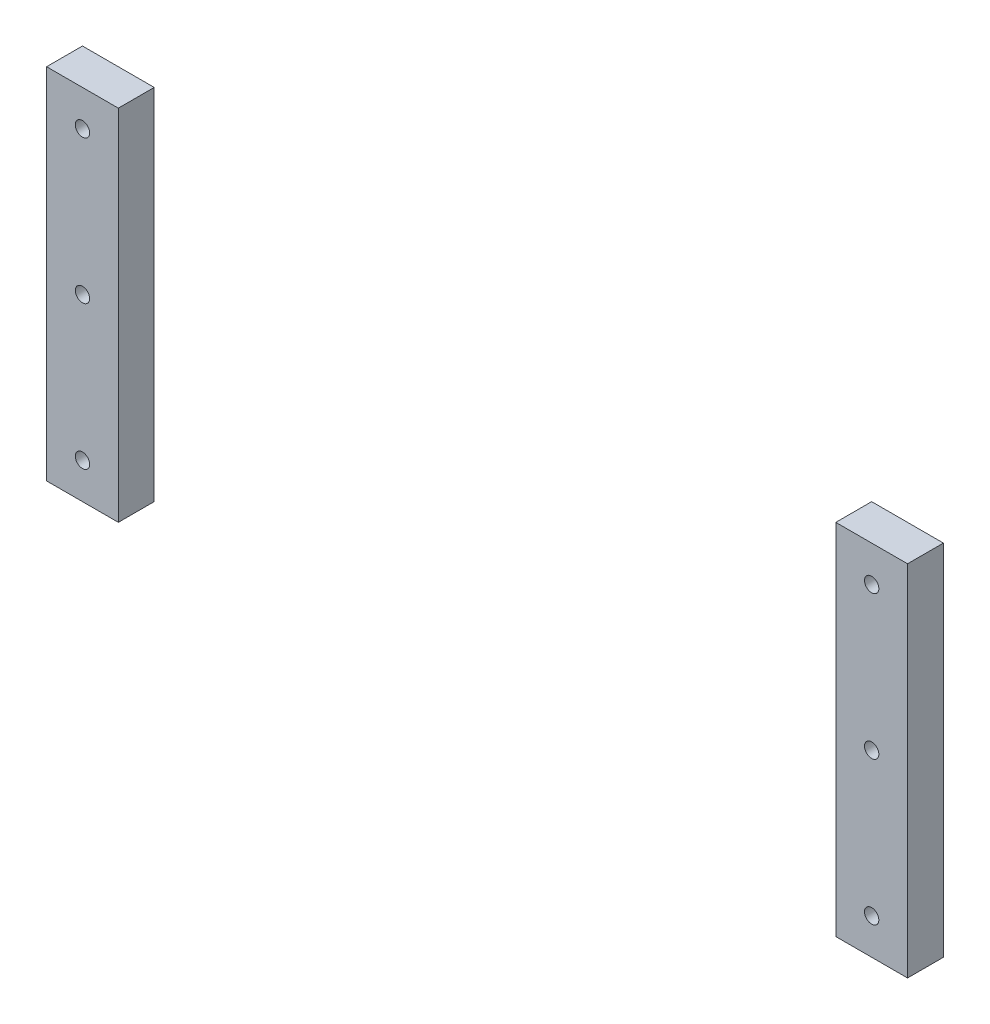
SolidWorks part; units mm, degrees
material "Cast Alloy Steel"
ref_plane "Front Plane" through (0, 0, 0) normal (0, 0, 1) x (1, 0, 0)
ref_plane "Top Plane" through (0, 0, 0) normal (0, 1, 0) x (1, 0, 0)
ref_plane "Right Plane" through (0, 0, 0) normal (1, 0, 0) x (0, 0, -1)
sketch "Sketch1" plane through (0, 0, 0) normal (0, 0, 1) x (1, 0, 0)
  line L0 (200, 0) -> (220, 0)
  line L1 (-20, 0) -> (0, 0)
  line L2 (-20, 0) -> (-20, 100)
  line L3 (-20, 100) -> (0, 100)
  line L4 (0, 0) -> (0, 100)
  line L5 (200, 0) -> (200, 100)
  line L6 (200, 100) -> (220, 100)
  line L7 (220, 0) -> (220, 100)
  line L8 (0, 100) -> (200, 100) construction
  dimension "D1" = 100
  dimension "D2" = 20
  dimension "D3" = 200
extrude "SupportExtrude" add sketch "Sketch1" along normal blind 10
ref_plane "Support Midplane" through (100, 0, 0) normal (1, 0, 0) x (0, 0, -1)
sketch "Sketch2" plane through (0, 0, 10) normal (0, 0, 1) x (1, 0, 0)
  line L0 (-20, 50) -> (0, 50) construction
  line L1 (-20, 100) -> (-20, 0) construction
  line L2 (0, 0) -> (0, 100) construction
  line L3 (-10, 100) -> (-10, 0) construction
  line L4 (0, 100) -> (-20, 100) construction
  line L5 (-20, 0) -> (0, 0) construction
  line L6 (-20, 10) -> (0, 10) construction
  line L7 (-20, 90) -> (0, 90) construction
  line L8 (100, -5.5) -> (100, 5.5) construction
  circle A1 centre (-10, 10) radius 2
  circle A2 centre (-10, 50) radius 2
  circle A3 centre (-10, 90) radius 2
  circle A4 centre (210, 10) radius 2
  circle A5 centre (210, 50) radius 2
  circle A6 centre (210, 90) radius 2
  point P22 (-10, 90)
  dimension "D1" = 10
  dimension "D2" = 4
  dimension "D3" = 10
extrude "Cut-Extrude1" cut sketch "Sketch2" against normal through all
